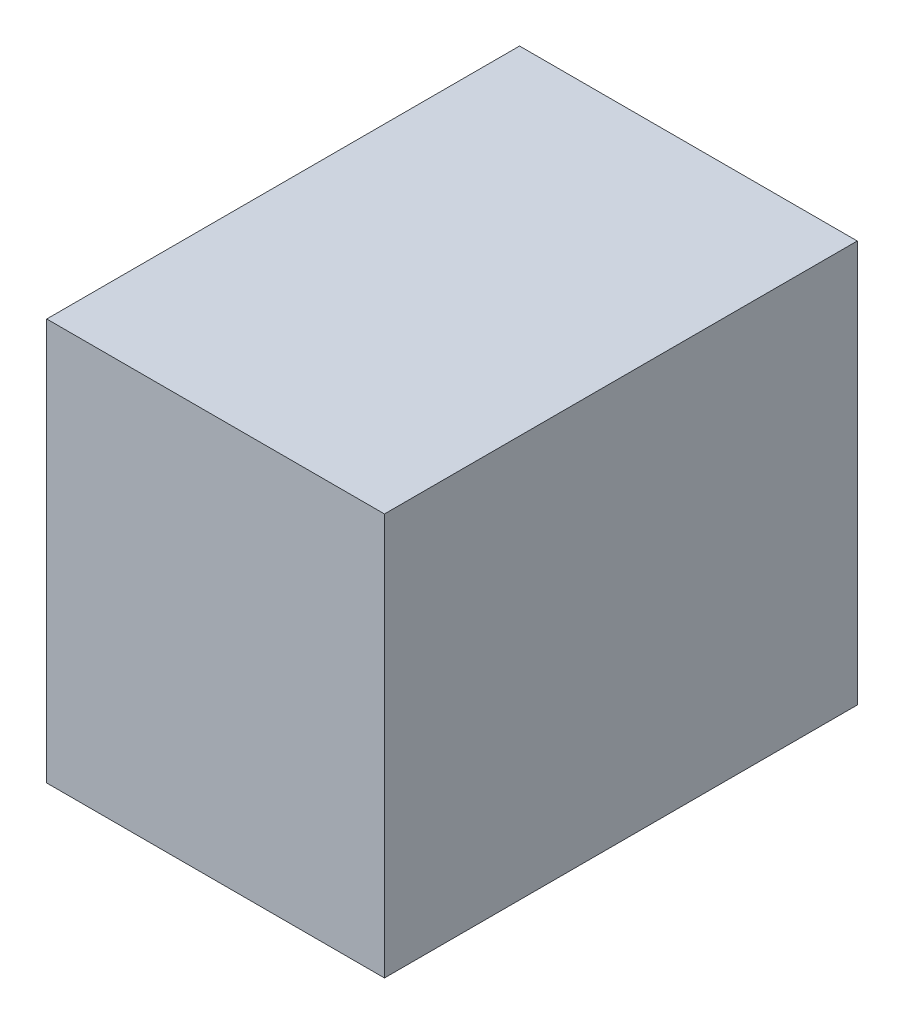
SolidWorks part; units mm, degrees
ref_plane "Front Plane" through (0, 0, 0) normal (0, 0, 1) x (1, 0, 0)
ref_plane "Top Plane" through (0, 0, 0) normal (0, 1, 0) x (1, 0, 0)
ref_plane "Right Plane" through (0, 0, 0) normal (1, 0, 0) x (0, 0, -1)
sketch "Sketch1" plane through (0, 0, 0) normal (0, 1, 0) x (1, 0, 0)
  line L1 (0, 0) -> (5, 0)
  line L2 (0, 0) -> (0, 7)
  line L3 (0, 7) -> (5, 7)
  line L4 (5, 0) -> (5, 7)
  dimension "D1" = 5
  dimension "D2" = 7
extrude "Boss-Extrude1" add sketch "Sketch1" along normal blind 5.95
